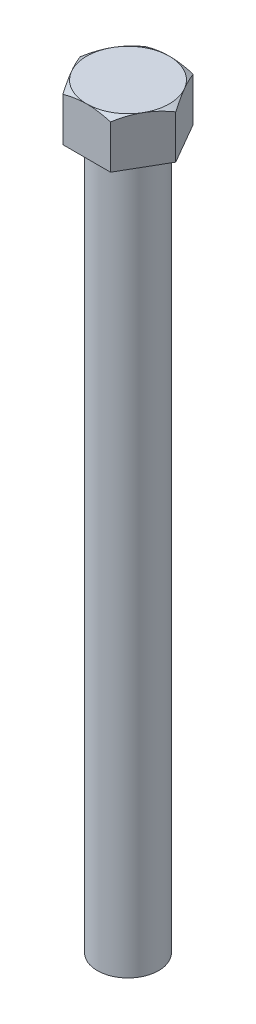
SolidWorks part; units mm, degrees
material "AISI 304"
ref_plane "Front Plane" through (0, 0, 0) normal (0, 0, 1) x (1, 0, 0)
ref_plane "Top Plane" through (0, 0, 0) normal (0, 1, 0) x (1, 0, 0)
ref_plane "Right Plane" through (0, 0, 0) normal (1, 0, 0) x (0, 0, -1)
sketch "Sketch1" plane through (0, 0, 0) normal (0, 1, 0) x (1, 0, 0)
  line L1 (-10.1036, -17.5) -> (10.1036, -17.5)
  line L2 (10.1036, -17.5) -> (20.2073, 0)
  line L3 (20.2073, 0) -> (10.1036, 17.5)
  line L4 (10.1036, 17.5) -> (-10.1036, 17.5)
  line L5 (-10.1036, 17.5) -> (-20.2073, 0)
  line L6 (-20.2073, 0) -> (-10.1036, -17.5)
  circle A0 centre (0, 0) radius 17.5 construction
  dimension "D1" = 35
extrude "Boss-Extrude1" add sketch "Sketch1" along normal blind 20
sketch "Sketch2" plane through (0, 20, 0) normal (0, 1, 0) x (1, 0, 0)
  circle A0 centre (0, 0) radius 17.5
extrude "Cut-Extrude1" cut sketch "Sketch2" against normal blind 20 draft 60 flip side to cut
sketch "Sketch3" plane through (0, 0, 0) normal (0, -1, 0) x (1, 0, 0)
  circle A0 centre (0, 0) radius 13
  dimension "D1" = 26
extrude "Boss-Extrude2" add sketch "Sketch3" along normal blind 300
